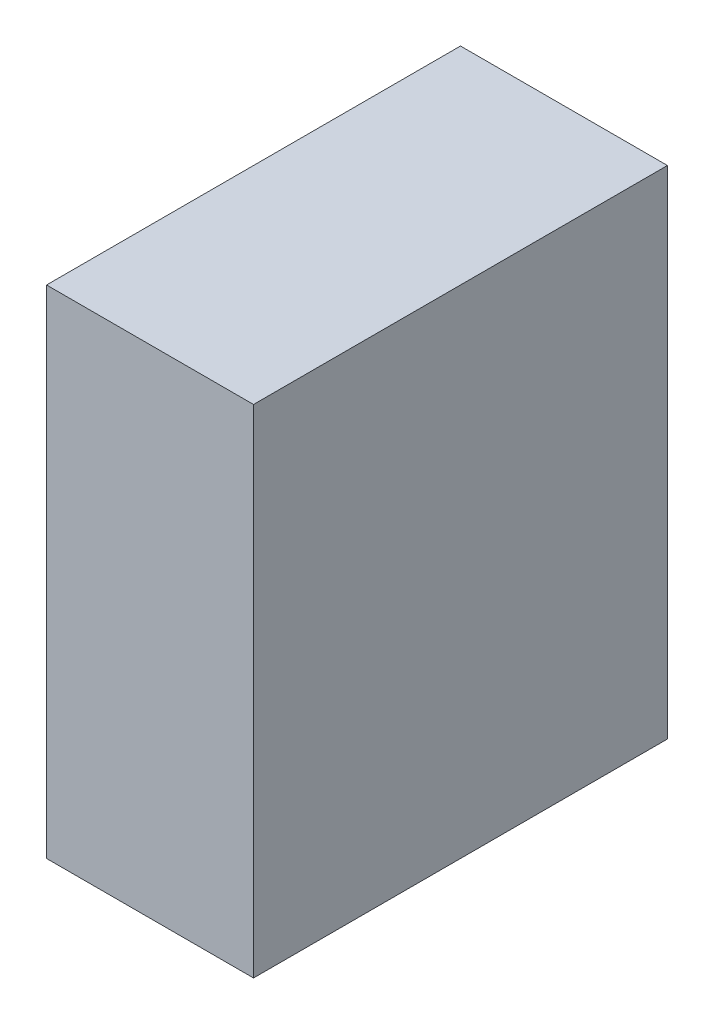
SolidWorks part; units mm, degrees
ref_plane "Front Plane" through (0, 0, 0) normal (0, 0, 1) x (1, 0, 0)
ref_plane "Top Plane" through (0, 0, 0) normal (0, 1, 0) x (1, 0, 0)
ref_plane "Right Plane" through (0, 0, 0) normal (1, 0, 0) x (0, 0, -1)
sketch "Sketch1" plane through (0, 0, 0) normal (1, 0, 0) x (0, 0, -1)
  line L0 (-10.0542, 4.4097) -> (-10.0542, -3.2103)
  line L1 (-10.0542, -3.2103) -> (-3.7042, -3.2103)
  line L2 (-3.7042, -3.2103) -> (-3.7042, 4.4097)
  line L3 (-3.7042, 4.4097) -> (-10.0542, 4.4097)
  dimension "D1" = 6.35
  dimension "D2" = 7.62
extrude "Boss-Extrude1" add sketch "Sketch1" along normal blind 3.175
